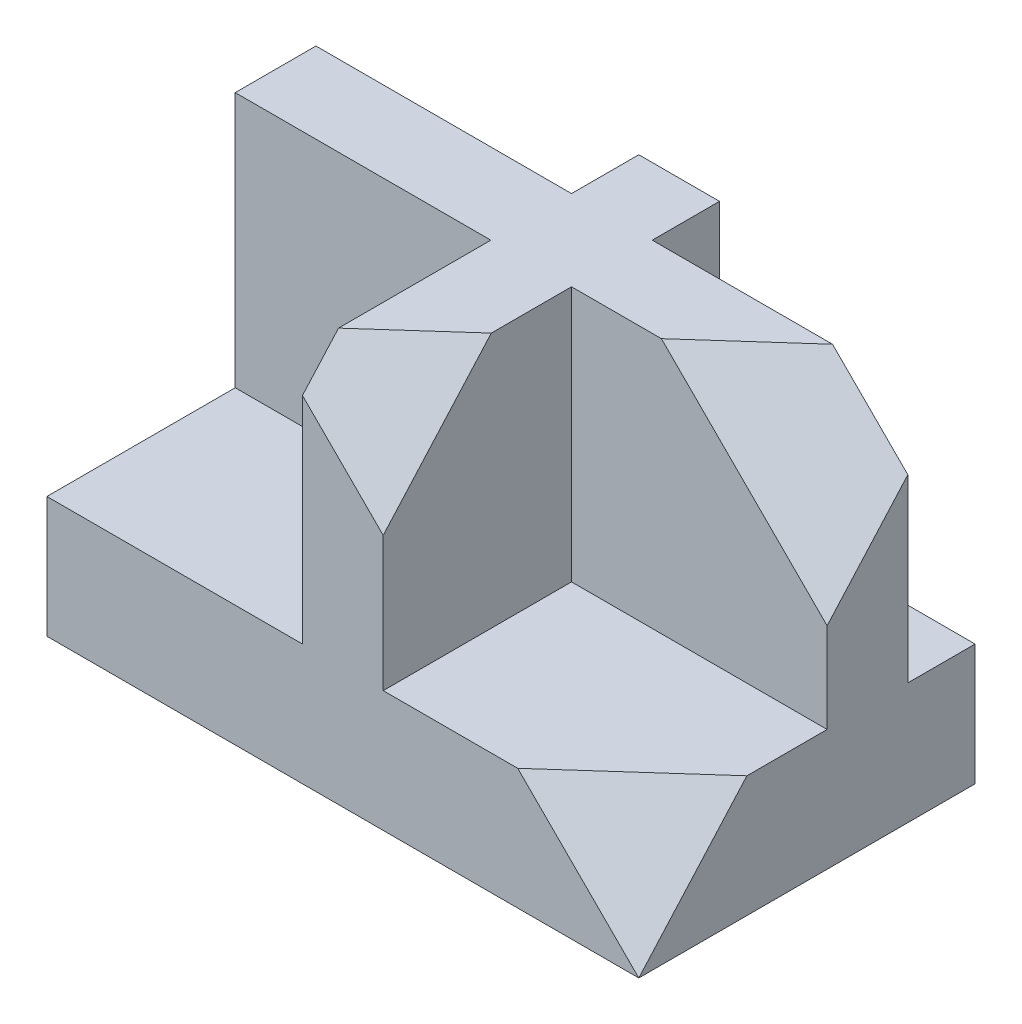
SolidWorks part; units mm, degrees
ref_plane "Front Plane" through (0, 0, 0) normal (0, 0, 1) x (1, 0, 0)
ref_plane "Top Plane" through (0, 0, 0) normal (0, 1, 0) x (1, 0, 0)
ref_plane "Right Plane" through (0, 0, 0) normal (1, 0, 0) x (0, 0, -1)
sketch "Sketch2" plane through (0, 0, 0) normal (0, 1, 0) x (1, 0, 0)
  line L1 (-44, 25) -> (44, 25)
  line L2 (-44, 25) -> (-44, -25)
  line L3 (-44, -25) -> (44, -25)
  line L4 (44, 25) -> (44, -25)
  line L5 (-44, 25) -> (44, -25) construction
  line L6 (-44, -25) -> (44, 25) construction
  point P0 (0, 0)
  dimension "D1" = 50
  dimension "D2" = 88
extrude "Boss-Extrude1" add sketch "Sketch2" along normal blind 18
sketch "Sketch3" plane through (0, 18, 0) normal (0, 1, 0) x (1, 0, 0)
  line L0 (-6, 25) -> (-6, 15)
  line L1 (44, 25) -> (-44, 25) construction
  line L2 (-6, 15) -> (-44, 15)
  line L3 (-44, 25) -> (-44, -25) construction
  line L4 (-44, 3) -> (-6, 3)
  line L5 (-6, 3) -> (-6, -25)
  line L6 (-44, -25) -> (44, -25) construction
  line L7 (6, 25) -> (6, 15)
  line L8 (6, 15) -> (44, 15)
  line L9 (44, -25) -> (44, 25) construction
  line L10 (6, -25) -> (6, 3)
  line L11 (6, 3) -> (44, 3)
  line L12 (-44, 15) -> (-44, 3)
  line L13 (-6, 25) -> (6, 25)
  line L14 (44, 15) -> (44, 3)
  line L15 (6, -25) -> (-6, -25)
  dimension "D1" = 12
  dimension "D2" = 38
  dimension "D3" = 12
  dimension "D4" = 10
extrude "Boss-Extrude2" add sketch "Sketch3" along normal blind 38
sketch "Sketch4" plane through (0, 56, 0) normal (0, 1, 0) x (1, 0, 0)
  line L1 (-44, 25) -> (44, 25)
  line L2 (-44, 25) -> (-44, -25) construction
  line L3 (-44, -25) -> (44, -25)
  line L4 (44, 25) -> (44, -25)
  line L5 (-44, 25) -> (44, -25) construction
  line L6 (-44, -25) -> (44, 25) construction
  point P1 (0, 0)
sketch "Sketch6" plane through (0, 0, 25) normal (0, 0, 1) x (1, 0, 0)
  line L0 (44, 0) -> (-12, 56)
  line L1 (-44, 56) -> (44, 56) construction
  line L2 (-44, 0) -> (44, 0) construction
  dimension "D1" = 45
ref_plane "Plane2" through (22.1239, 22.1239, 24.7788) normal (0.5543, 0.5543, 0.6208) x (0.8323, -0.3692, -0.4135)
sketch "Sketch7" plane through (22.1239, 22.1239, 24.7788) normal (0.5543, 0.5543, 0.6208) x (0.8323, -0.3692, -0.4135)
  line L0 (-40.9995, 25.1221) -> (26.2839, -16.6504)
  line L1 (26.2839, -16.6504) -> (26.2839, 58.4229)
  line L2 (26.2839, 58.4229) -> (-40.9995, 25.1221)
extrude "Cut-Extrude14" cut sketch "Sketch7" along normal blind 38
